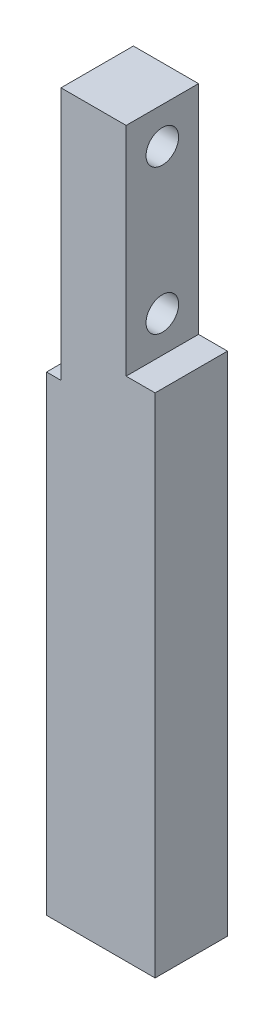
SolidWorks part; units mm, degrees
ref_plane "Front Plane" through (0, 0, 0) normal (0, 0, 1) x (1, 0, 0)
ref_plane "Top Plane" through (0, 0, 0) normal (0, 1, 0) x (1, 0, 0)
ref_plane "Right Plane" through (0, 0, 0) normal (1, 0, 0) x (0, 0, -1)
sketch "Sketch1" plane through (0, 0, 0) normal (0, 0, 1) x (1, 0, 0)
  line L0 (-7.612, 62.794) -> (1.388, 62.794)
  line L1 (1.388, 62.794) -> (1.388, 32.794)
  line L2 (1.388, 32.794) -> (5.388, 32.794)
  line L3 (5.388, 32.794) -> (5.388, -37.206)
  line L4 (5.388, -37.206) -> (-9.612, -37.206)
  line L5 (-9.612, -37.206) -> (-9.612, 27.794)
  line L6 (-9.612, 27.794) -> (-7.612, 27.794)
  line L7 (-7.612, 27.794) -> (-7.612, 62.794)
  dimension "D1" = 9
  dimension "D2" = 30
  dimension "D3" = 70
  dimension "D4" = 15
  dimension "D5" = 65
  dimension "D6" = 2
extrude "Boss-Extrude1" add sketch "Sketch1" along normal blind 10
sketch "Sketch2" plane through (-7.612, 0, 0) normal (-1, 0, 0) x (0, 0, 1)
  line L0 (10, 62.794) -> (0, 62.794) construction
  circle A0 centre (5, 57.794) radius 4
  circle A1 centre (5, 37.794) radius 4
  point P4 (0, 0)
  dimension "D1" = 8
  dimension "D2" = 20
  dimension "D3" = 5
extrude "Cut-Extrude1" cut sketch "Sketch2" against normal blind 4.5
sketch "Sketch3" plane through (-3.112, 0, 0) normal (-1, 0, 0) x (0, 0, 1)
  circle A0 centre (5, 37.794) radius 2.25
  circle A1 centre (5, 57.794) radius 2.25
  dimension "D1" = 4.5
  dimension "D2" = 4.5
extrude "Cut-Extrude2" cut sketch "Sketch3" against normal through all
hole_wizard "M4x0.7 Tapped Hole1" positions "Sketch4" profile "Sketch5" tap size "M4x0.7" standard "ANSI Metric"
sketch "Sketch4" plane through (-9.612, 0, 0) normal (-1, 0, 0) x (0, 0, 1)
  line L0 (0, 27.794) -> (0, -37.206) construction
  line L1 (10, -37.206) -> (0, -37.206) construction
  point P0 (5, 2.794)
  point P2 (5, -27.206)
  point P4 (0, 0)
  dimension "D1" = 5
  dimension "D2" = 30
  dimension "D3" = 10
sketch "Sketch5" plane through (-9.612, 2.794, 5) normal (0, 1, 0) x (0, 0, 1)
  line L0 (0, 0) -> (0, 8.9914)
  line L1 (0, 8.9914) -> (1.65, 8)
  line L2 (1.65, 8) -> (1.65, 0)
  line L5 (1.65, 0) -> (0, 0)
  line L10 (0, 8.9914) -> (-1.65, 8) construction
  line L11 (0, -6.35) -> (0, 107.95) construction
  dimension "Tap Drill Dia." = 3.3
  dimension "Tap Drill Depth" = 8
  dimension "Drill Angle" = 118
cosmetic thread "Hole Thread1" parameters "D1"=8, "D2"=4
cosmetic thread "Hole Thread2" parameters "D1"=8, "D2"=4
